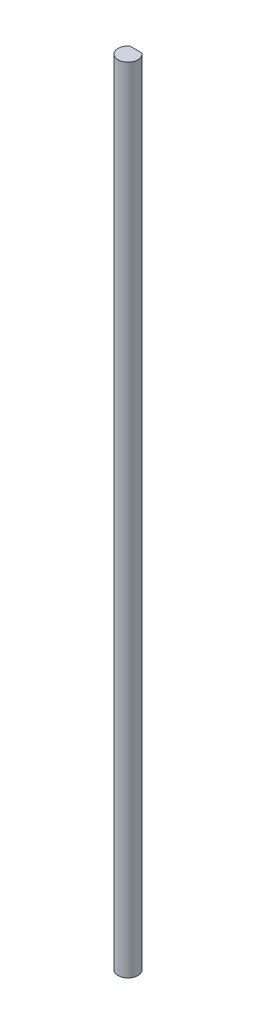
SolidWorks part; units mm, degrees
ref_plane "Front Plane" through (0, 0, 0) normal (0, 0, 1) x (1, 0, 0)
ref_plane "Top Plane" through (0, 0, 0) normal (0, 1, 0) x (1, 0, 0)
ref_plane "Right Plane" through (0, 0, 0) normal (1, 0, 0) x (0, 0, -1)
sketch "Sketch1" plane through (0, 0, 0) normal (0, 1, 0) x (1, 0, 0)
  line L0 (-1.905, 2.54) -> (1.905, 2.54)
  arc A0 (-1.905, 2.54) -> (1.905, 2.54) centre (0, 0) ccw
  dimension "D1" = 6.35
  dimension "D2" = 2.54
extrude "Boss-Extrude1" add sketch "Sketch1" along normal blind 254
